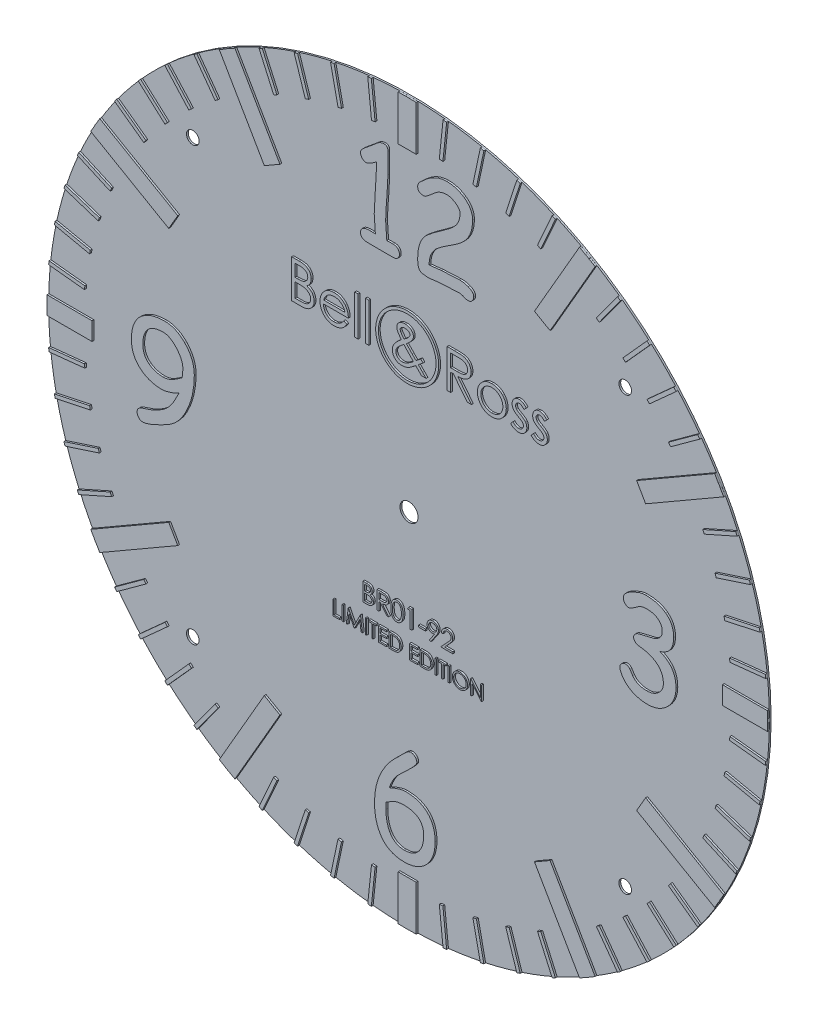
SolidWorks part; units mm, degrees
ref_plane "Alzado" through (0, 0, 0) normal (0, 0, 1) x (1, 0, 0)
ref_plane "Planta" through (0, 0, 0) normal (0, 1, 0) x (1, 0, 0)
ref_plane "Vista lateral" through (0, 0, 0) normal (1, 0, 0) x (0, 0, -1)
sketch "Croquis1" plane through (0, 0, 0) normal (0, 0, 1) x (1, 0, 0)
  circle A0 centre (0, 0) radius 20
  dimension "D1" = 40
extrude "Saliente-Extruir1" add sketch "Croquis1" along normal blind 0.1
sketch "Croquis14" plane through (0, 0, 0.1) normal (0, 0, 1) x (1, 0, 0)
  line L0 (0, 0) -> (0, 20) construction
  line L1 (0, 0) -> (20, 0) construction
  line L2 (10, 0) -> (10, 10) construction
  line L3 (10, 10) -> (10, 13) construction
  line L4 (10, 13) -> (12, 13) construction
  circle A0 centre (0, 0) radius 20 construction
  circle A1 centre (12, 12) radius 0.35
  circle A2 centre (-12, 12) radius 0.35
  circle A3 centre (12, -12) radius 0.35
  circle A4 centre (-12, -12) radius 0.35
  point P10 (12, 12)
  dimension "D1" = 0.7
  dimension "D2" = 3
  dimension "D3" = 2
  dimension "D4" = 1
extrude "Cortar-Extruir4" cut sketch "Croquis14" against normal blind 10
sketch "Croquis9" plane through (0, 0, 0.1) normal (0, 0, 1) x (1, 0, 0)
  line L0 (0, 20) -> (0, 18) construction
  line L2 (-0.1, 20) -> (0.1, 20)
  line L3 (-0.1, 20) -> (-0.1, 18)
  line L4 (-0.1, 18) -> (0.1, 18)
  line L5 (0.1, 20) -> (0.1, 18)
  line L6 (-0.1, 20) -> (0.1, 18) construction
  line L7 (-0.1, 18) -> (0.1, 20) construction
  circle A0 centre (0, 0) radius 20 construction
  point P6 (0, 19)
  dimension "D1" = 2
  dimension "D2" = 0.2
  dimension "D3" = 2
extrude "Saliente-Extruir7" add sketch "Croquis9" along normal blind 0.1
pattern_circular "MatrizC2" count 60 over 360 about axis through (0, 0, 0) along (0, 0, 1) of "Saliente-Extruir7"
sketch "Croquis2" plane through (0, 0, 0.1) normal (0, 0, 1) x (1, 0, 0)
  line L0 (0, 0) -> (0, 20) construction
  line L2 (-0.5, 19.9937) -> (0.5, 19.9937)
  line L3 (-0.5, 19.9937) -> (-0.5, 14.9937)
  line L4 (-0.5, 14.9937) -> (0.5, 14.9937)
  line L5 (0.5, 19.9937) -> (0.5, 14.9937)
  circle A0 centre (0, 0) radius 20 construction
  point P9 (0, 19.9937)
  dimension "D1" = 1
  dimension "D2" = 5
extrude "Saliente-Extruir2" add sketch "Croquis2" along normal blind 0.1
pattern_circular "MatrizC1" count 12 over 360 about axis through (0, 0, 0) along (0, 0, 1) of "Saliente-Extruir2"
sketch "Croquis3" plane through (0, 0, 0.2) normal (0, 0, 1) x (1, 0, 0)
  line L0 (-0.5, 19.9937) -> (-0.5, 14.9937) construction
  line L1 (-0.5, 17.4937) -> (0.5, 17.4937)
  line L2 (-0.5, 17.4937) -> (-0.5, 14.9937)
  line L3 (-0.5, 14.9937) -> (0.5, 14.9937)
  line L4 (0.5, 17.4937) -> (0.5, 14.9937)
extrude "Cortar-Extruir1" cut sketch "Croquis3" against normal blind 0.1
sketch "Croquis4" plane through (0, 0, 0.2) normal (0, 0, 1) x (1, 0, 0)
  line L0 (19.9937, 0.5) -> (14.9937, 0.5) construction
  line L1 (17.4937, 0.5) -> (14.9937, 0.5)
  line L2 (17.4937, 0.5) -> (17.4937, -0.5)
  line L3 (17.4937, -0.5) -> (14.9937, -0.5)
  line L4 (14.9937, 0.5) -> (14.9937, -0.5)
  line L5 (14.9937, -0.5) -> (19.9937, -0.5) construction
  line L6 (-14.9937, 0.5) -> (-19.9937, 0.5) construction
  line L7 (-17.4937, 0.5) -> (-14.9937, 0.5)
  line L8 (-17.4937, 0.5) -> (-17.4937, -0.5)
  line L9 (-17.4937, -0.5) -> (-14.9937, -0.5)
  line L10 (-14.9937, 0.5) -> (-14.9937, -0.5)
  line L11 (0.5, -19.9937) -> (0.5, -14.9937) construction
  line L12 (-0.5, -14.9937) -> (0.5, -14.9937)
  line L13 (-0.5, -14.9937) -> (-0.5, -17.4937)
  line L14 (-0.5, -17.4937) -> (0.5, -17.4937)
  line L15 (0.5, -14.9937) -> (0.5, -17.4937)
extrude "Cortar-Extruir2" cut sketch "Croquis4" against normal blind 0.1
sketch "Croquis5" plane through (0, 0, 0.2) normal (0, 0, 1) x (1, 0, 0)
  line L0 (0, 20) -> (0, 12) construction
  line L1 (-3, 12) -> (3, 12) construction
  circle A0 centre (0, 0) radius 20 construction
  text T0 "12" font "Comic Sans MS" height in points 18
  point P8 (0, 12)
  dimension "D1" = 8
  dimension "D2" = 6
extrude "Saliente-Extruir3" add sketch "Croquis5" along normal blind 0.1 separate body
sketch "Croquis6" plane through (0, 0, 0.2) normal (0, 0, 1) x (1, 0, 0)
  line L0 (0, -20) -> (0, -16.5) construction
  line L1 (-3, -16.5) -> (3, -16.5) construction
  circle A0 centre (0, 0) radius 20 construction
  text T0 "6" font "Comic Sans MS" height in points 18
  point P8 (0, -16.5)
  dimension "D1" = 3.5
  dimension "D2" = 6
extrude "Saliente-Extruir4" add sketch "Croquis6" along normal blind 0.1 separate body
sketch "Croquis7" plane through (0, 0, 0.2) normal (0, 0, 1) x (1, 0, 0)
  line L2 (-16.4937, 2.4551) -> (-16.4937, -2.5449) construction
  line L3 (-16.4937, -2.5449) -> (-10.4937, -2.5449) construction
  text T0 "9" font "Comic Sans MS" height in points 18
  dimension "D2" = 5
  dimension "D3" = 6
extrude "Saliente-Extruir5" add sketch "Croquis7" along normal blind 0.1 separate body
sketch "Croquis8" plane through (0, 0, 0.2) normal (0, 0, 1) x (1, 0, 0)
  line L2 (16.4937, 2.2997) -> (16.4937, -2.2997) construction
  line L3 (16.4937, -2.2997) -> (10.4937, -2.2997) construction
  text T0 "3" font "Comic Sans MS" height in points 18
  point P7 (16.4937, 0)
  dimension "D2" = 6
extrude "Saliente-Extruir6" add sketch "Croquis8" along normal blind 0.1 separate body
sketch "Croquis11" plane through (0, 0, 0.1) normal (0, 0, 1) x (1, 0, 0)
  line L0 (0, 0) -> (0, 7.98) construction
  circle A0 centre (0, 7.98) radius 1.75
  circle A1 centre (0, 7.98) radius 1.6
  dimension "D2" = 3.5
  dimension "D3" = 3.2
  dimension "D1" = 7.98
extrude "Saliente-Extruir9" add sketch "Croquis11" along normal blind 0.1
sketch "Croquis10" plane through (0, 0, 0.1) normal (0, 0, 1) x (1, 0, 0)
  line L0 (0, 0) -> (0, 7) construction
  line L1 (-7.5, 7) -> (7.5, 7) construction
  text T0 " Bell & Ross" font "Century Gothic" height in points 8
  point P5 (0, 7)
  dimension "D1" = 7
  dimension "D2" = 15
extrude "Saliente-Extruir8" add sketch "Croquis10" along normal blind 0.1
sketch "Croquis12" plane through (0, 0, 0.1) normal (0, 0, 1) x (1, 0, 0)
  line L0 (0, 0) -> (0, -7) construction
  line L1 (-7.5, -7) -> (7.5, -7) construction
  line L2 (-7.5, -5.5) -> (7.5, -5.5) construction
  text T0 "LIMITED EDITION" font "Century Gothic" height 0.8
  text T1 "BR01-92" font "Century Gothic" height 1
  point P0 (0, 0)
  point P6 (0, -7)
  point P8 (0, -5.5)
  dimension "D1" = 7
  dimension "D2" = 15
  dimension "D3" = 1.5
extrude "Saliente-Extruir10" add sketch "Croquis12" along normal blind 0.1
sketch "Croquis13" plane through (0, 0, 0.1) normal (0, 0, 1) x (1, 0, 0)
  line L0 (13.235, 7.0639) -> (17.5651, 9.5639) construction
  circle A0 centre (0, 0) radius 0.5
  point P0 (0, 0)
  point P1 (15.4, 8.3139)
  dimension "D1" = 1
extrude "Cortar-Extruir3" cut sketch "Croquis13" against normal blind 0.2
